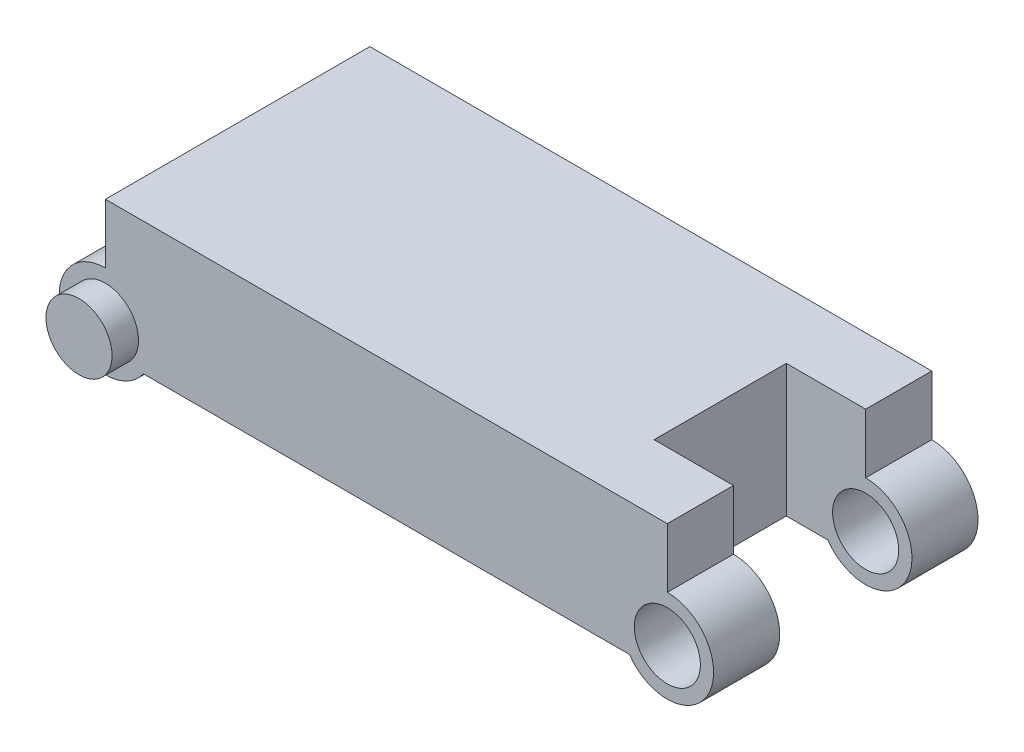
SolidWorks part; units mm, degrees
ref_plane "Front Plane" through (0, 0, 0) normal (0, 0, 1) x (1, 0, 0)
ref_plane "Top Plane" through (0, 0, 0) normal (0, 1, 0) x (1, 0, 0)
ref_plane "Right Plane" through (0, 0, 0) normal (1, 0, 0) x (0, 0, -1)
sketch "Sketch1" plane through (0, 0, 0) normal (0, 0, 1) x (1, 0, 0)
  line L1 (28.7228, -20) -> (396.2772, -20)
  line L2 (0, 35) -> (0, 80)
  line L3 (0, 80) -> (425, 80)
  line L4 (425, 35) -> (425, 80)
  arc A0 (0, 35) -> (28.7228, -20) centre (0, 0) ccw
  arc A1 (396.2772, -20) -> (425, 35) centre (425, 0) ccw
  circle A2 centre (425, 0) radius 25
  dimension "D1" = 70
  dimension "D5" = 70
  dimension "D7" = 50
  dimension "D2" = 425
  dimension "D3" = 20
  dimension "D4" = 80
  dimension "D6" = 20
extrude "Boss-Extrude1" add sketch "Sketch1" along normal blind 200
sketch "Sketch2" plane through (0, 0, 200) normal (0, 0, 1) x (1, 0, 0)
  circle A0 centre (0, 0) radius 25
  dimension "D1" = 50
extrude "Boss-Extrude2" add sketch "Sketch2" along normal blind 20 and the other way blind 220
sketch "Sketch3" plane through (0, 0, 200) normal (0, 0, 1) x (1, 0, 0)
  line L0 (425, 80) -> (0, 80) construction
  line L1 (365, 80) -> (493.2932, 80)
  line L2 (365, 80) -> (365, -40)
  line L3 (365, -40) -> (493.2932, -40)
  line L4 (493.2932, 80) -> (493.2932, -40)
  line L5 (425, 35) -> (425, 80) construction
  dimension "D1" = 60
  dimension "D2" = 120
extrude "Cut-Extrude1" cut sketch "Sketch3" against normal blind 100 from offset 50
